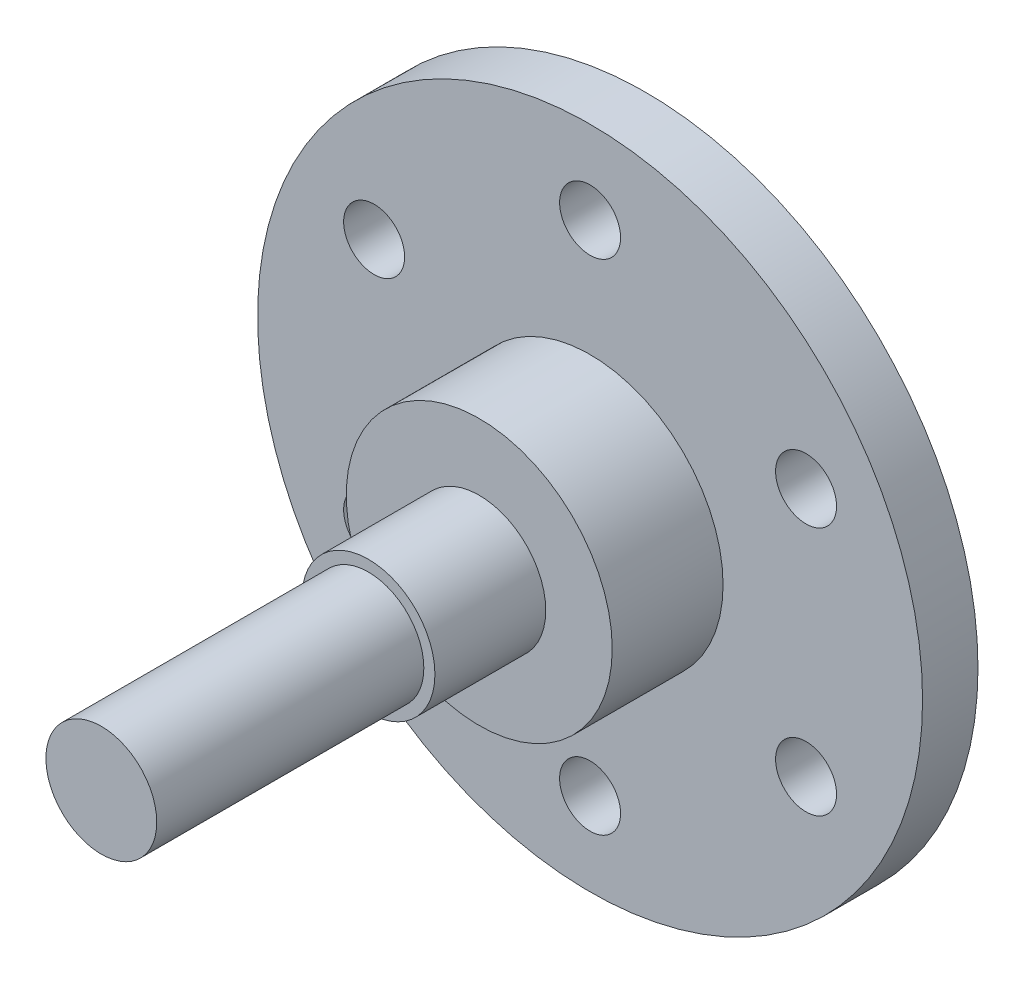
SolidWorks part; units mm, degrees
ref_plane "前视基准面" through (0, 0, 0) normal (0, 0, 1) x (1, 0, 0)
ref_plane "上视基准面" through (0, 0, 0) normal (0, 1, 0) x (1, 0, 0)
ref_plane "右视基准面" through (0, 0, 0) normal (1, 0, 0) x (0, 0, -1)
sketch "草图1" plane through (0, 0, 0) normal (0, 0, 1) x (1, 0, 0)
  line L0 (0, 0) -> (0, 13.9022) construction
  line L1 (0, 0) -> (0, 55.2697) construction
  circle A0 centre (0, 0) radius 30
  circle A1 centre (0, 0) radius 22.5 construction
  circle A2 centre (0, 22.5) radius 2.75
  circle A3 centre (19.4856, 11.25) radius 2.75
  circle A4 centre (19.4856, -11.25) radius 2.75
  circle A5 centre (0, -22.5) radius 2.75
  circle A6 centre (-19.4856, -11.25) radius 2.75
  circle A7 centre (-19.4856, 11.25) radius 2.75
  point P20 (0, 0)
  dimension "D1" = 6
extrude "凸台-拉伸1" add sketch "草图1" along normal blind 5
sketch "草图2" plane through (0, 0, 5) normal (0, 0, 1) x (1, 0, 0)
  circle A0 centre (0, 0) radius 12
extrude "凸台-拉伸2" add sketch "草图2" along normal blind 10
sketch "草图3" plane through (0, 0, 15) normal (0, 0, 1) x (1, 0, 0)
  circle A0 centre (0, 0) radius 6
extrude "凸台-拉伸3" add sketch "草图3" along normal blind 10
sketch "草图5" plane through (0, 0, 25) normal (0, 0, 1) x (1, 0, 0)
  circle A0 centre (0, 0) radius 5
extrude "凸台-拉伸4" add sketch "草图5" along normal blind 24.1
